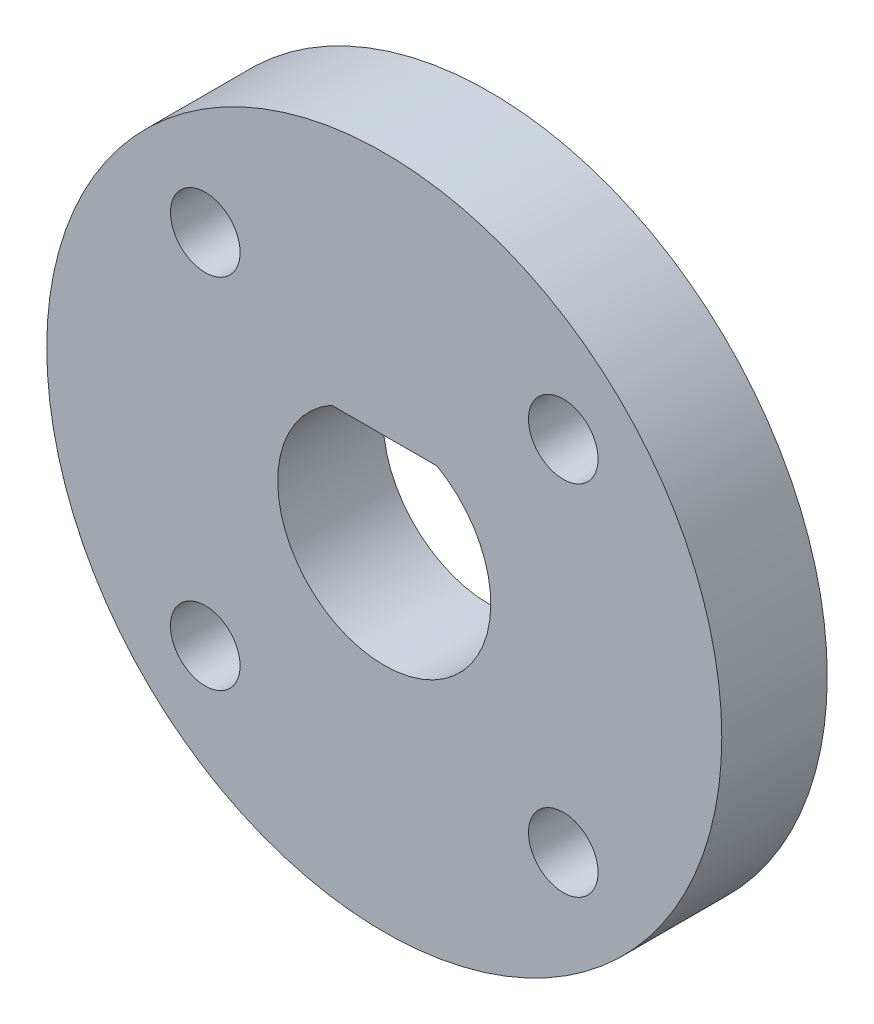
SolidWorks part; units mm, degrees
material "Plain Carbon Steel"
ref_plane "Front Plane" through (0, 0, 0) normal (0, 0, 1) x (1, 0, 0)
ref_plane "Top Plane" through (0, 0, 0) normal (0, 1, 0) x (1, 0, 0)
ref_plane "Right Plane" through (0, 0, 0) normal (1, 0, 0) x (0, 0, -1)
sketch "Sketch1" plane through (0, 0, 0) normal (0, 0, 1) x (1, 0, 0)
  line L0 (-2.5, 4.3878) -> (2.5, 4.3878)
  line L1 (-2.5, 4.3301) -> (2.5, 4.3301) construction
  line L2 (-8.4853, -8.4853) -> (8.4853, 8.4853) construction
  line L3 (-8.4853, 8.4853) -> (8.4853, -8.4853) construction
  line L4 (0, -1000) -> (0, 49000) construction
  circle A0 centre (0, 0) radius 5.05
  circle A1 centre (0, 0) radius 12 construction
  circle A2 centre (0, 0) radius 16
  circle A3 centre (0, 0) radius 5 construction
  point P12 (0, 0)
  point P16 (0, 0)
  dimension "D1" = 10.1
  dimension "D3" = 24
  dimension "D4" = 32
  dimension "D6" = 10
  dimension "D2" = 5
  dimension "D5" = 5
  dimension "D7" = 45
extrude "Boss-Extrude1" add sketch "Sketch1" along normal mid plane 5 contours A2 A0 | L0 A0
sketch "Sketch2" plane through (0, 0, 2.5) normal (0, 0, 1) x (1, 0, 0)
  point P9 (8.4853, 8.4853)
  point P12 (-8.4853, 8.4853)
  point P15 (-8.4853, -8.4853)
  point P18 (8.4853, -8.4853)
  point P22 (0, 0)
  point P23 (0, 0)
  point P24 (0, 0)
  point P25 (0, 0)
hole_wizard "Tap Drill for M4x0.7 Tap1" positions "Sketch2" profile "Sketch3" hole size "M4x0.7" standard "ANSI Metric" end condition through all
sketch "Sketch3" plane through (8.4853, 8.4853, 2.5) normal (1, 0, 0) x (0, -1, 0)
  line L0 (0, 0) -> (0, 5)
  line L1 (0, 5) -> (1.65, 5)
  line L2 (1.65, 5) -> (1.65, 0)
  line L5 (1.65, 0) -> (0, 0)
  line L11 (0, -6.35) -> (0, 107.95) construction
  dimension "Thru Hole Dia." = 3.3
  dimension "Thru Hole Depth" = 5
